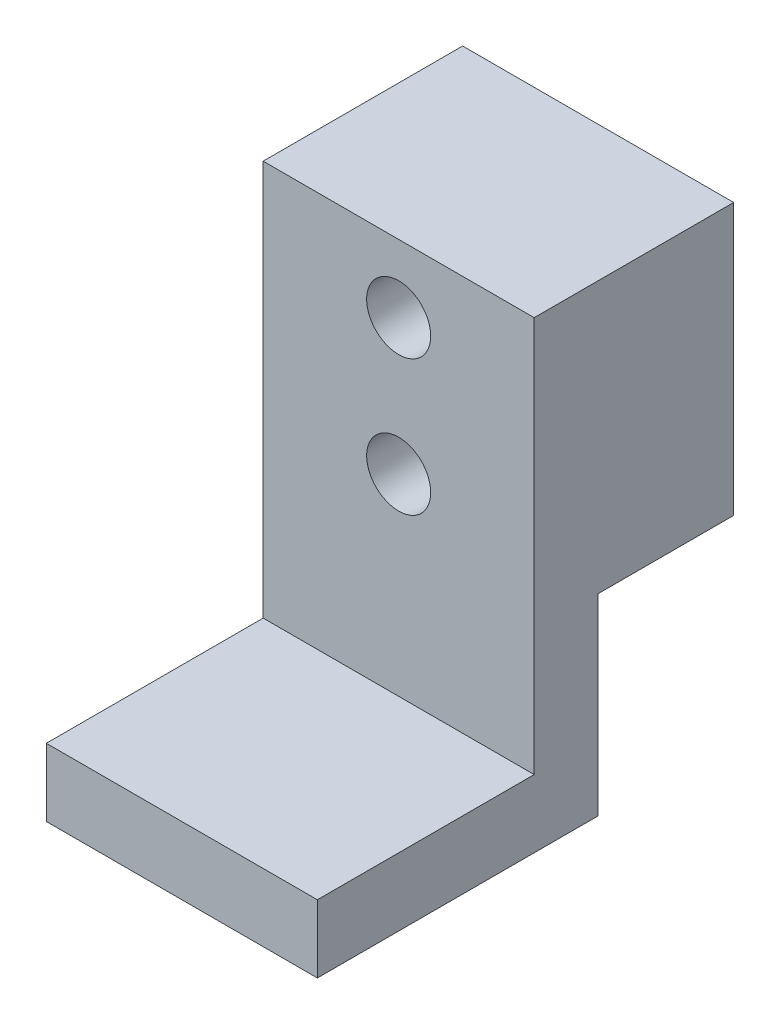
SolidWorks part; units mm, degrees
ref_plane "Front Plane" through (0, 0, 0) normal (0, 0, 1) x (1, 0, 0)
ref_plane "Top Plane" through (0, 0, 0) normal (0, 1, 0) x (1, 0, 0)
ref_plane "Right Plane" through (0, 0, 0) normal (1, 0, 0) x (0, 0, -1)
sketch "Sketch1" plane through (0, 0, 0) normal (1, 0, 0) x (0, 0, -1)
  line L0 (0, 12.7) -> (0, 0)
  line L1 (0, 0) -> (-6.35, 0)
  line L2 (-6.35, 0) -> (-6.35, -9.017)
  line L3 (-6.35, -9.017) -> (-19.5072, -9.017)
  line L4 (-19.5072, -9.017) -> (-19.5072, -5.842)
  line L5 (-19.5072, -5.842) -> (-9.3472, -5.842)
  line L6 (-9.3472, -5.842) -> (-9.3472, 12.7)
  line L7 (-9.3472, 12.7) -> (0, 12.7)
  dimension "D1" = 6.35
  dimension "D2" = 2.9972
  dimension "D3" = 5.842
  dimension "D4" = 3.175
  dimension "D5" = 12.7
  dimension "D6" = 10.16
extrude "Boss-Extrude1" add sketch "Sketch1" along normal mid plane 12.7
sketch "Sketch2" plane through (0, 0, 9.3472) normal (0, 0, 1) x (1, 0, 0)
  line L0 (0, 9.525) -> (0, 0) construction
  line L1 (6.35, 0) -> (-6.35, 0) construction
  line L2 (6.35, 0) -> (-6.35, 0) construction
  circle A0 centre (0, 9.525) radius 1.5
  circle A1 centre (0, 3.175) radius 1.5
  dimension "D1" = 3
  dimension "D2" = 6.35
  dimension "D3" = 3.175
extrude "Cut-Extrude1" cut sketch "Sketch2" against normal through all
equation "\"bottomThickness\"= .220in"
equation "\"wallThickness\"= .118in"
equation "\"D3@Sketch1\"=\"bottomThickness\"+.01in"
